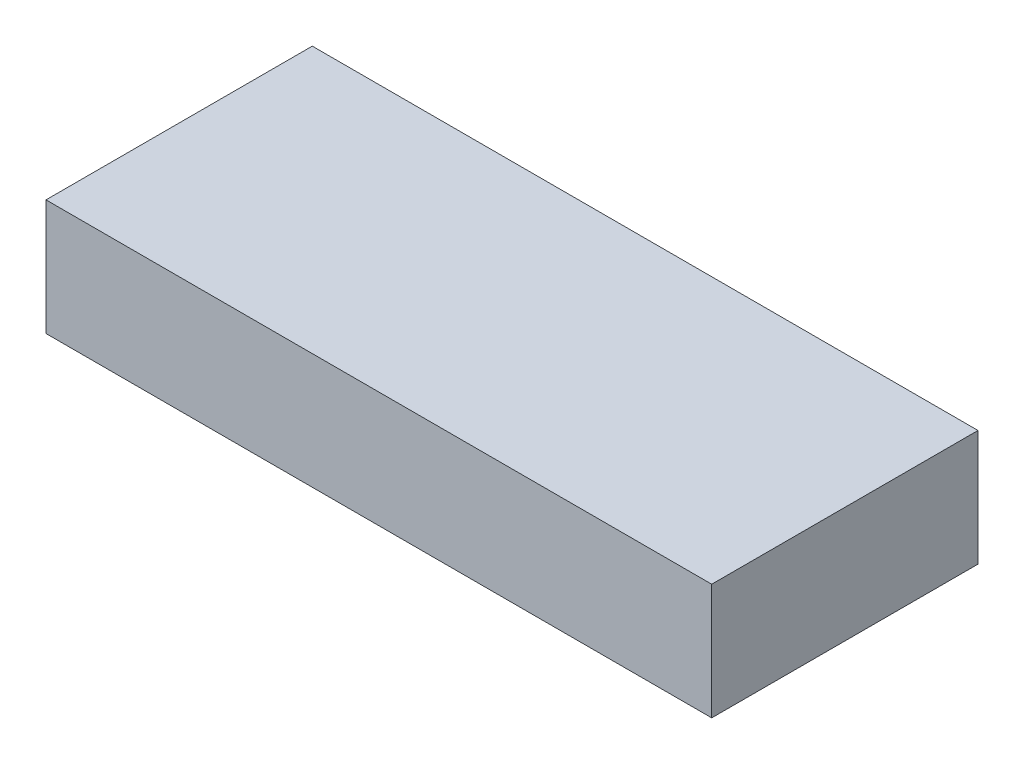
SolidWorks part; units mm, degrees
ref_plane "前视基准面" through (0, 0, 0) normal (0, 0, 1) x (1, 0, 0)
ref_plane "上视基准面" through (0, 0, 0) normal (0, 1, 0) x (1, 0, 0)
ref_plane "右视基准面" through (0, 0, 0) normal (1, 0, 0) x (0, 0, -1)
sketch "草图1" plane through (0, 0, 0) normal (0, 1, 0) x (1, 0, 0)
  line L0 (-57.5, -23) -> (-57.5, 23)
  line L1 (-57.5, 23) -> (57.5, 23)
  line L2 (57.5, 23) -> (57.5, -23)
  line L3 (57.5, -23) -> (-57.5, -23)
  line L4 (-57.5, -23) -> (57.5, 23) construction
  line L5 (-57.5, 23) -> (57.5, -23) construction
  point P3 (0, 0)
  dimension "D1" = 46
  dimension "D2" = 115
extrude "凸台-拉伸1" add sketch "草图1" along normal blind 20
